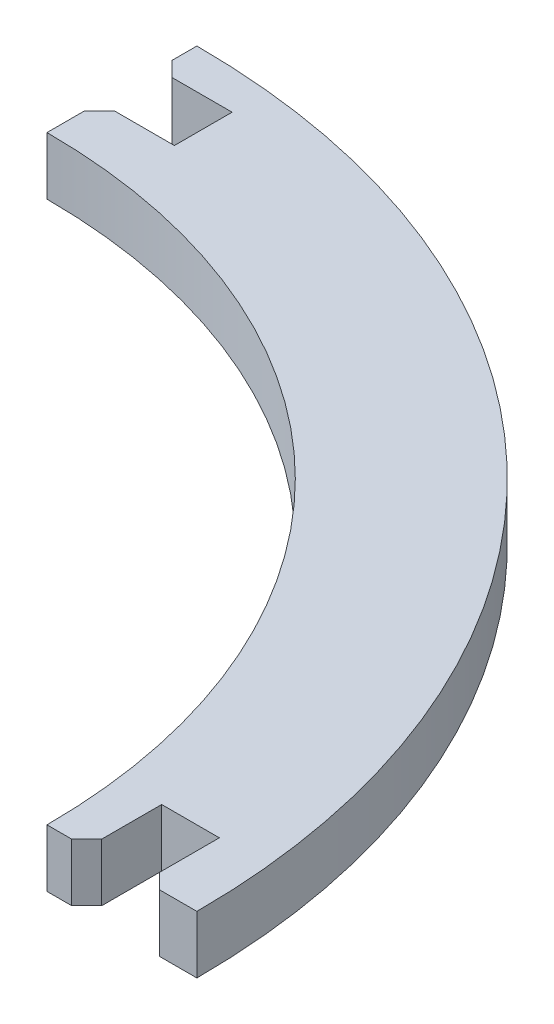
SolidWorks part; units mm, degrees
ref_plane "Front" through (0, 0, 0) normal (0, 0, 1) x (1, 0, 0)
ref_plane "Top" through (0, 0, 0) normal (0, 1, 0) x (1, 0, 0)
ref_plane "Right" through (0, 0, 0) normal (1, 0, 0) x (0, 0, -1)
sketch "Sketch1" plane through (0, 0, 0) normal (0, 1, 0) x (1, 0, 0)
  line L0 (0, 0) -> (0, 48.5255) construction
  line L1 (0, 0) -> (38.1883, 0) construction
  line L2 (0, 50) -> (0, 47.35)
  line L3 (40, 0) -> (42.65, 0)
  line L4 (0, 45.425) -> (6.2717, 45.425) construction
  line L5 (0, 47.35) -> (5, 47.35)
  line L6 (44.575, 0) -> (44.575, 6.7904) construction
  line L7 (0, 43.5) -> (5, 43.5)
  line L8 (5, 47.35) -> (5, 43.5)
  line L9 (0, 43.5) -> (0, 40)
  line L10 (46.5, 0) -> (50, 0)
  line L12 (42.65, 0) -> (42.65, 5)
  line L13 (42.65, 5) -> (46.5, 5)
  line L14 (46.5, 0) -> (46.5, 5)
  circle A0 centre (0, 0) radius 50 construction
  circle A1 centre (0, 0) radius 40 construction
  arc A2 (0, 40) -> (40, 0) centre (0, 0) cw
  arc A3 (0, 50) -> (50, 0) centre (0, 0) cw
  dimension "D1" = 100
  dimension "D3" = 3.85
  dimension "D4" = 5
  dimension "D5" = 5
  dimension "D6" = 3.85
  dimension "D2" = 10
extrude "Boss-Extrude1" add sketch "Sketch1" along normal blind 3.85 contours A2 L3 L12 L13 L14 L10 A3 L2 L5 L8 L7 L9
chamfer "Chamfer1" distance 1 angle 45 4 edges at (42.65, 1.925, 0) (46.5, 1.925, 0) (0, 1.925, -43.5) (0, 1.925, -47.35)
equation "\"D6@Sketch1\" = \"thick\""
equation "\"D5@Sketch1\"=\"entrance\""
equation "\"D3@Sketch1\" = \"thick\""
equation "\"D4@Sketch1\"=\"entrance\""
equation "\"D1@Boss-Extrude1\"= \"thick\""
equation "\"entrance\"=5"
equation "\"thick\"=3.85"
